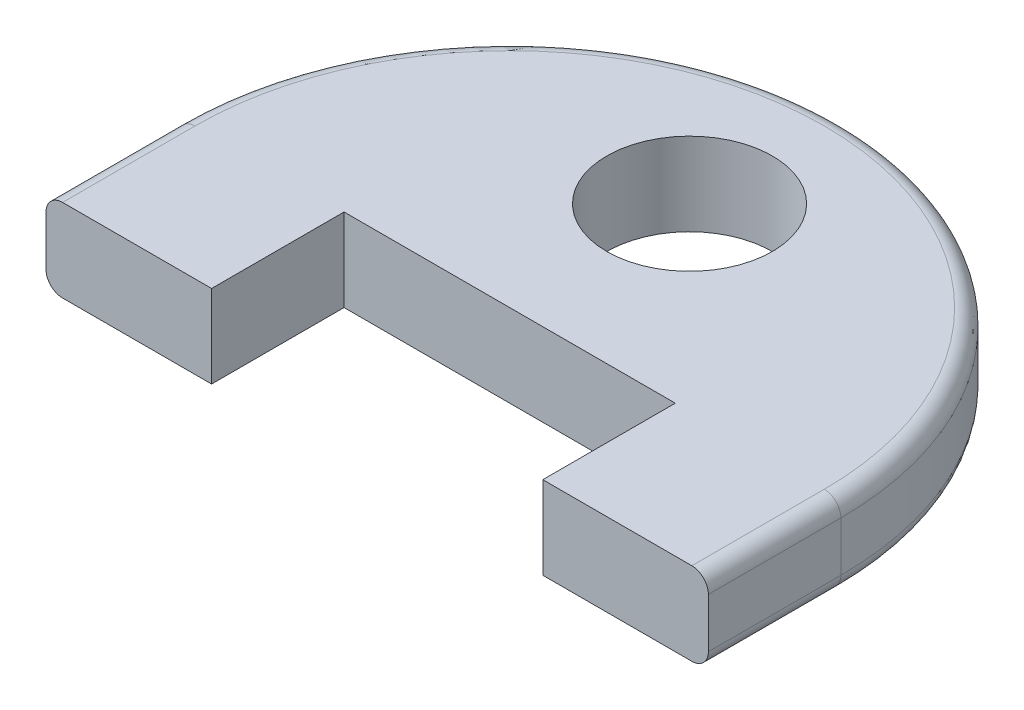
SolidWorks part; units mm, degrees
ref_plane "Front Plane" through (0, 0, 0) normal (0, 0, 1) x (1, 0, 0)
ref_plane "Top Plane" through (0, 0, 0) normal (0, 1, 0) x (1, 0, 0)
ref_plane "Right Plane" through (0, 0, 0) normal (1, 0, 0) x (0, 0, -1)
sketch "Sketch1" plane through (0, 0, 0) normal (0, 1, 0) x (1, 0, 0)
  line L1 (-25.4, -10.16) -> (-12.7, -10.16)
  line L2 (-25.4, -10.16) -> (-25.4, 0)
  line L4 (25.4, -10.16) -> (25.4, 0)
  line L8 (-12.7, -10.16) -> (-12.7, 0)
  line L9 (-12.7, 0) -> (12.7, 0)
  line L10 (12.7, -10.16) -> (12.7, 0)
  line L11 (12.7, -10.16) -> (25.4, -10.16)
  arc A0 (-25.4, 0) -> (25.4, 0) centre (0, 0) cw
  point P0 (0, 0)
  dimension "D1" = 25.4
  dimension "D2" = 12.7
  dimension "D3" = 12.7
  dimension "D4" = 10.16
extrude "Boss-Extrude1" add sketch "Sketch1" along normal blind 6.35
fillet "Fillet2" radius 1.27 6 edges at (25.4, 0, 5.08) (-25.4, 0, 5.08) (25.4, 6.35, 5.08) (-25.4, 6.35, 5.08) (0, 0, -25.4) (0, 6.35, -25.4)
sketch "Sketch2" plane through (0, 6.35, 0) normal (0, 1, 0) x (1, 0, 0)
  circle A0 centre (0, 13.7961) radius 6.35
  dimension "D1" = 12.7
extrude "Cut-Extrude1" cut sketch "Sketch2" against normal through all
